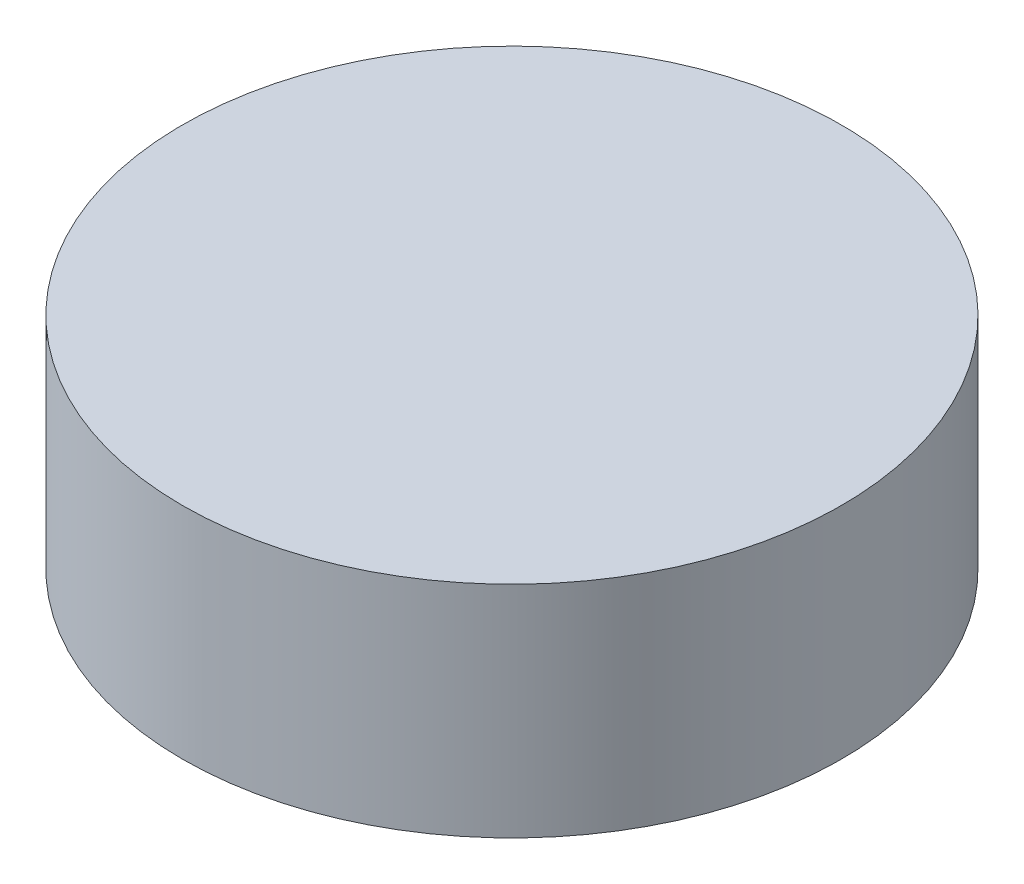
SolidWorks part; units mm, degrees
ref_plane "Front" through (0, 0, 0) normal (0, 0, 1) x (1, 0, 0)
ref_plane "Top" through (0, 0, 0) normal (0, 1, 0) x (1, 0, 0)
ref_plane "Right" through (0, 0, 0) normal (1, 0, 0) x (0, 0, -1)
sketch "Sketch2" plane through (0, 0, 0) normal (0, 1, 0) x (1, 0, 0)
  circle A0 centre (0, 0) radius 15
  dimension "D1" = 30
extrude "Boss-Extrude1" add sketch "Sketch2" along normal mid plane 10
sketch "Sketch4" plane through (0, -5, 0) normal (0, -1, 0) x (-1, 0, 0)
  circle A0 centre (0, 0) radius 3
  dimension "D1" = 6
extrude "Cut-Extrude2" cut sketch "Sketch4" against normal blind 3
